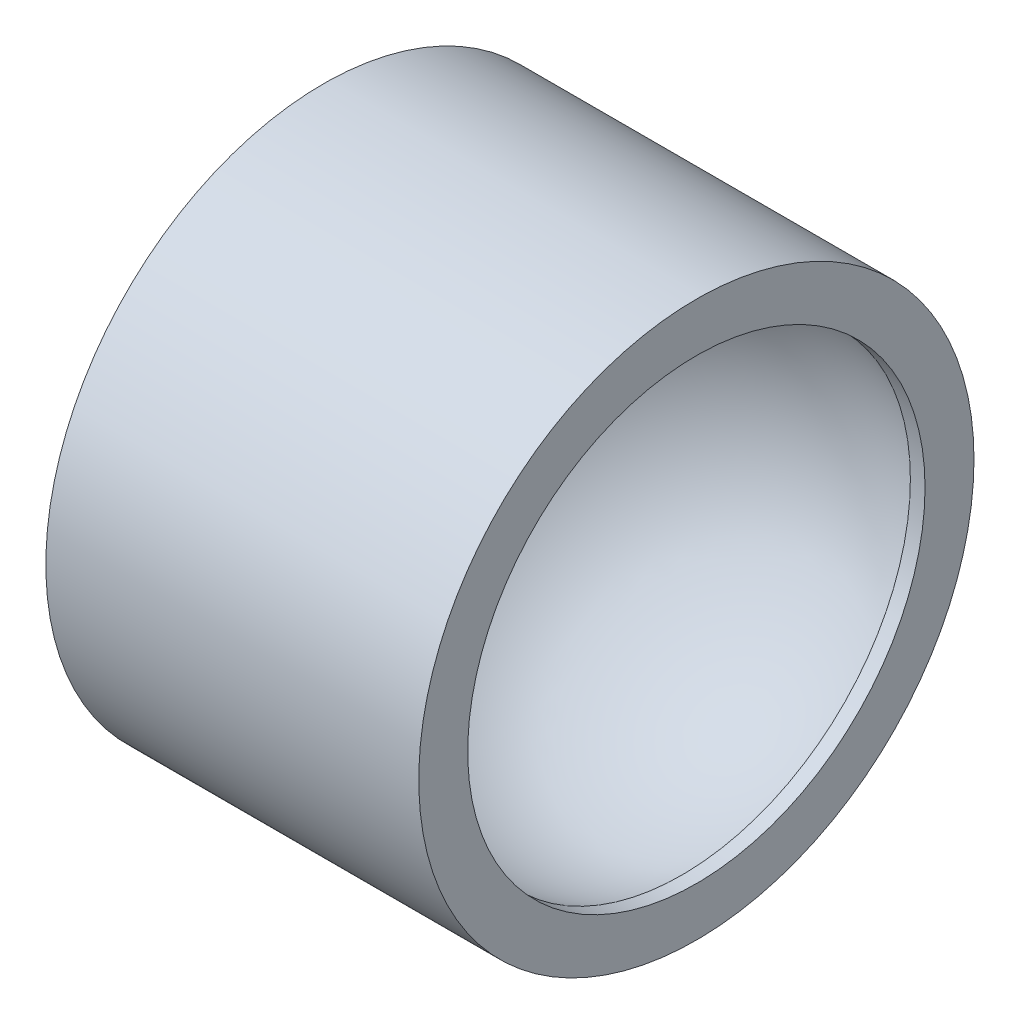
SolidWorks part; units mm, degrees
ref_plane "Alzado" through (0, 0, 0) normal (0, 0, 1) x (1, 0, 0)
ref_plane "Planta" through (0, 0, 0) normal (0, 1, 0) x (1, 0, 0)
ref_plane "Vista lateral" through (0, 0, 0) normal (1, 0, 0) x (0, 0, -1)
sketch "Croquis1" plane through (0, 0, 0) normal (0, 1, 0) x (1, 0, 0)
  line L0 (-10, 0) -> (-12.141, 0)
  line L1 (3.4828, 11.6308) -> (-12.141, 11.6308)
  line L2 (3.4828, 11.6308) -> (3.4828, 9.5797)
  line L3 (3.4828, 9.5797) -> (2.8686, 9.5797)
  line L4 (-12.141, 11.6308) -> (-12.141, 0)
  arc A0 (2.8686, 9.5797) -> (-10, 0) centre (0, 0) ccw
  dimension "D1" = 10
revolve "Revolución1" add sketch "Croquis1" angle 360 about L0
